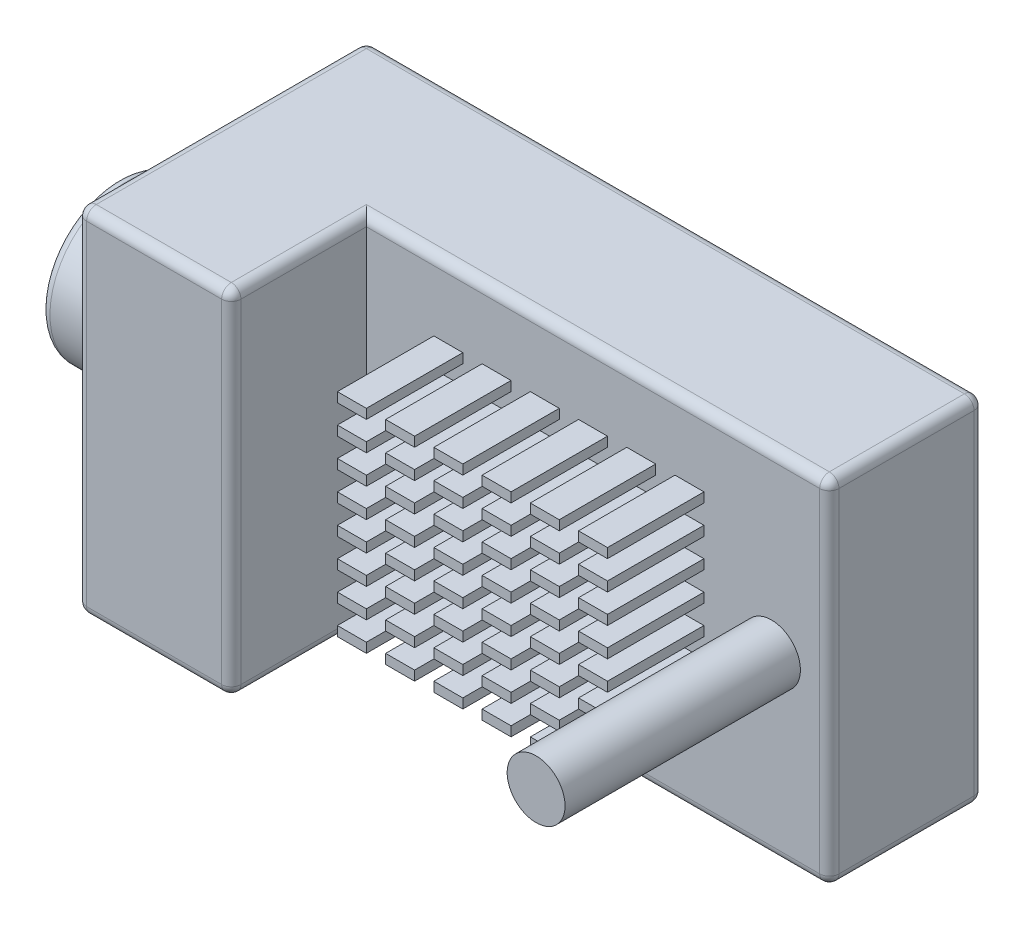
SolidWorks part; units mm, degrees
ref_plane "前基準面" through (0, 0, 0) normal (0, 0, 1) x (1, 0, 0)
ref_plane "上基準面" through (0, 0, 0) normal (0, 1, 0) x (1, 0, 0)
ref_plane "右基準面" through (0, 0, 0) normal (1, 0, 0) x (0, 0, -1)
sketch "草圖1" plane through (0, 0, 0) normal (0, 0, 1) x (1, 0, 0)
  line L1 (-16, 9.15) -> (16, 9.15)
  line L2 (-16, 9.15) -> (-16, -9.15)
  line L3 (-16, -9.15) -> (16, -9.15)
  line L4 (16, 9.15) -> (16, -9.15)
  line L5 (-16, 9.15) -> (16, -9.15) construction
  line L6 (-16, -9.15) -> (16, 9.15) construction
  point P0 (0, 0)
  dimension "D1" = 18.3
  dimension "D2" = 32
extrude "填料-伸長1" add sketch "草圖1" along normal mid plane 8
sketch "草圖2" plane through (0, 0, 4) normal (0, 0, 1) x (1, 0, 0)
  line L0 (-16, -9.15) -> (16, -9.15) construction
  line L1 (-16, 9.15) -> (-8, 9.15)
  line L2 (-16, 9.15) -> (-16, -9.15)
  line L3 (-16, -9.15) -> (-8, -9.15)
  line L4 (-8, 9.15) -> (-8, -9.15)
  dimension "D1" = 8
extrude "填料-伸長2" add sketch "草圖2" along normal blind 7
sketch "草圖4" plane through (-16, 0, 0) normal (-1, 0, 0) x (0, 0, 1)
  line L0 (11, 9.15) -> (11, -9.15) construction
  line L1 (11, -9.15) -> (-4, -9.15) construction
  circle A0 centre (3.5, 0) radius 2.5
  point P4 (11, 0)
  point P7 (3.5, -9.15)
  dimension "D1" = 5
extrude "填料-伸長3" add sketch "草圖4" along normal blind 2
sketch "草圖5" plane through (-18, 0, 0) normal (-1, 0, 0) x (0, 0, 1)
  circle A0 centre (3.5, 0) radius 4
  dimension "D1" = 8
extrude "填料-伸長4" add sketch "草圖5" along normal blind 3.4
sketch "草圖6" plane through (0, 0, 4) normal (0, 0, 1) x (1, 0, 0)
  line L0 (-8, -9.15) -> (-8, 9.15) construction
  line L1 (-5, 6) -> (10, 6)
  line L2 (-5, 6) -> (-5, -6)
  line L3 (-5, -6) -> (10, -6)
  line L4 (10, 6) -> (10, -6)
  line L5 (-5, 6) -> (10, -6) construction
  line L6 (-5, -6) -> (10, 6) construction
  line L7 (16, -9.15) -> (16, 9.15) construction
  point P0 (2.5, 0)
  point P9 (16, 0)
  dimension "D1" = 15
  dimension "D2" = 12
  dimension "D3" = 3
extrude "填料-伸長5" add sketch "草圖6" along normal blind 5
sketch "草圖7" plane through (0, 0, 9) normal (0, 0, 1) x (1, 0, 0)
  line L0 (-2, 5.5) -> (-2, 5)
  line L1 (-4.5, 5.5) -> (-3, 5.5)
  line L2 (-4.5, 5.5) -> (-4.5, 5)
  line L3 (-4.5, 5) -> (-3, 5)
  line L4 (-3, 5.5) -> (-3, 5)
  line L5 (-2, 5.5) -> (-0.5, 5.5)
  line L6 (-0.5, 5.5) -> (-0.5, 5)
  line L7 (-2, 5) -> (-0.5, 5)
  line L8 (0.5, 5.5) -> (0.5, 5)
  line L9 (0.5, 5.5) -> (2, 5.5)
  line L10 (2, 5.5) -> (2, 5)
  line L11 (0.5, 5) -> (2, 5)
  line L12 (3, 5.5) -> (3, 5)
  line L13 (3, 5.5) -> (4.5, 5.5)
  line L14 (4.5, 5.5) -> (4.5, 5)
  line L15 (3, 5) -> (4.5, 5)
  line L16 (5.5, 5.5) -> (5.5, 5)
  line L17 (5.5, 5.5) -> (7, 5.5)
  line L18 (7, 5.5) -> (7, 5)
  line L19 (5.5, 5) -> (7, 5)
  line L20 (8, 5.5) -> (8, 5)
  line L21 (8, 5.5) -> (9.5, 5.5)
  line L22 (9.5, 5.5) -> (9.5, 5)
  line L23 (8, 5) -> (9.5, 5)
  line L24 (-4.5, 4) -> (-4.5, 3.5)
  line L25 (-4.5, 4) -> (-3, 4)
  line L26 (-3, 4) -> (-3, 3.5)
  line L27 (-4.5, 3.5) -> (-3, 3.5)
  line L28 (-2, 4) -> (-2, 3.5)
  line L29 (-2, 3.5) -> (-0.5, 3.5)
  line L30 (-0.5, 4) -> (-0.5, 3.5)
  line L31 (-2, 4) -> (-0.5, 4)
  line L32 (0.5, 4) -> (0.5, 3.5)
  line L33 (0.5, 3.5) -> (2, 3.5)
  line L34 (2, 4) -> (2, 3.5)
  line L35 (0.5, 4) -> (2, 4)
  line L36 (3, 4) -> (3, 3.5)
  line L37 (3, 3.5) -> (4.5, 3.5)
  line L38 (4.5, 4) -> (4.5, 3.5)
  line L39 (3, 4) -> (4.5, 4)
  line L40 (5.5, 4) -> (5.5, 3.5)
  line L41 (5.5, 3.5) -> (7, 3.5)
  line L42 (7, 4) -> (7, 3.5)
  line L43 (5.5, 4) -> (7, 4)
  line L44 (8, 4) -> (8, 3.5)
  line L45 (8, 3.5) -> (9.5, 3.5)
  line L46 (9.5, 4) -> (9.5, 3.5)
  line L47 (8, 4) -> (9.5, 4)
  line L48 (-4.5, 2.5) -> (-4.5, 2)
  line L49 (-4.5, 2.5) -> (-3, 2.5)
  line L50 (-3, 2.5) -> (-3, 2)
  line L51 (-4.5, 2) -> (-3, 2)
  line L52 (-2, 2.5) -> (-2, 2)
  line L53 (-2, 2) -> (-0.5, 2)
  line L54 (-0.5, 2.5) -> (-0.5, 2)
  line L55 (-2, 2.5) -> (-0.5, 2.5)
  line L56 (0.5, 2.5) -> (0.5, 2)
  line L57 (0.5, 2) -> (2, 2)
  line L58 (2, 2.5) -> (2, 2)
  line L59 (0.5, 2.5) -> (2, 2.5)
  line L60 (3, 2.5) -> (3, 2)
  line L61 (3, 2) -> (4.5, 2)
  line L62 (4.5, 2.5) -> (4.5, 2)
  line L63 (3, 2.5) -> (4.5, 2.5)
  line L64 (5.5, 2.5) -> (5.5, 2)
  line L65 (5.5, 2) -> (7, 2)
  line L66 (7, 2.5) -> (7, 2)
  line L67 (5.5, 2.5) -> (7, 2.5)
  line L68 (8, 2.5) -> (8, 2)
  line L69 (8, 2) -> (9.5, 2)
  line L70 (9.5, 2.5) -> (9.5, 2)
  line L71 (8, 2.5) -> (9.5, 2.5)
  line L72 (-4.5, 1) -> (-4.5, 0.5)
  line L73 (-4.5, 1) -> (-3, 1)
  line L74 (-3, 1) -> (-3, 0.5)
  line L75 (-4.5, 0.5) -> (-3, 0.5)
  line L76 (-2, 1) -> (-2, 0.5)
  line L77 (-2, 0.5) -> (-0.5, 0.5)
  line L78 (-0.5, 1) -> (-0.5, 0.5)
  line L79 (-2, 1) -> (-0.5, 1)
  line L80 (0.5, 1) -> (0.5, 0.5)
  line L81 (0.5, 0.5) -> (2, 0.5)
  line L82 (2, 1) -> (2, 0.5)
  line L83 (0.5, 1) -> (2, 1)
  line L84 (3, 1) -> (3, 0.5)
  line L85 (3, 0.5) -> (4.5, 0.5)
  line L86 (4.5, 1) -> (4.5, 0.5)
  line L87 (3, 1) -> (4.5, 1)
  line L88 (5.5, 1) -> (5.5, 0.5)
  line L89 (5.5, 0.5) -> (7, 0.5)
  line L90 (7, 1) -> (7, 0.5)
  line L91 (5.5, 1) -> (7, 1)
  line L92 (8, 1) -> (8, 0.5)
  line L93 (8, 0.5) -> (9.5, 0.5)
  line L94 (9.5, 1) -> (9.5, 0.5)
  line L95 (8, 1) -> (9.5, 1)
  line L96 (-4.5, -0.5) -> (-4.5, -1)
  line L97 (-4.5, -0.5) -> (-3, -0.5)
  line L98 (-3, -0.5) -> (-3, -1)
  line L99 (-4.5, -1) -> (-3, -1)
  line L100 (-2, -0.5) -> (-2, -1)
  line L101 (-2, -1) -> (-0.5, -1)
  line L102 (-0.5, -0.5) -> (-0.5, -1)
  line L103 (-2, -0.5) -> (-0.5, -0.5)
  line L104 (0.5, -0.5) -> (0.5, -1)
  line L105 (0.5, -1) -> (2, -1)
  line L106 (2, -0.5) -> (2, -1)
  line L107 (0.5, -0.5) -> (2, -0.5)
  line L108 (3, -0.5) -> (3, -1)
  line L109 (3, -1) -> (4.5, -1)
  line L110 (4.5, -0.5) -> (4.5, -1)
  line L111 (3, -0.5) -> (4.5, -0.5)
  line L112 (5.5, -0.5) -> (5.5, -1)
  line L113 (5.5, -1) -> (7, -1)
  line L114 (7, -0.5) -> (7, -1)
  line L115 (5.5, -0.5) -> (7, -0.5)
  line L116 (8, -0.5) -> (8, -1)
  line L117 (8, -1) -> (9.5, -1)
  line L118 (9.5, -0.5) -> (9.5, -1)
  line L119 (8, -0.5) -> (9.5, -0.5)
  line L120 (-4.5, -2) -> (-4.5, -2.5)
  line L121 (-4.5, -2) -> (-3, -2)
  line L122 (-3, -2) -> (-3, -2.5)
  line L123 (-4.5, -2.5) -> (-3, -2.5)
  line L124 (-2, -2) -> (-2, -2.5)
  line L125 (-2, -2.5) -> (-0.5, -2.5)
  line L126 (-0.5, -2) -> (-0.5, -2.5)
  line L127 (-2, -2) -> (-0.5, -2)
  line L128 (0.5, -2) -> (0.5, -2.5)
  line L129 (0.5, -2.5) -> (2, -2.5)
  line L130 (2, -2) -> (2, -2.5)
  line L131 (0.5, -2) -> (2, -2)
  line L132 (3, -2) -> (3, -2.5)
  line L133 (3, -2.5) -> (4.5, -2.5)
  line L134 (4.5, -2) -> (4.5, -2.5)
  line L135 (3, -2) -> (4.5, -2)
  line L136 (5.5, -2) -> (5.5, -2.5)
  line L137 (5.5, -2.5) -> (7, -2.5)
  line L138 (7, -2) -> (7, -2.5)
  line L139 (5.5, -2) -> (7, -2)
  line L140 (8, -2) -> (8, -2.5)
  line L141 (8, -2.5) -> (9.5, -2.5)
  line L142 (9.5, -2) -> (9.5, -2.5)
  line L143 (8, -2) -> (9.5, -2)
  line L144 (-4.5, -3.5) -> (-4.5, -4)
  line L145 (-4.5, -3.5) -> (-3, -3.5)
  line L146 (-3, -3.5) -> (-3, -4)
  line L147 (-4.5, -4) -> (-3, -4)
  line L148 (-2, -3.5) -> (-2, -4)
  line L149 (-2, -4) -> (-0.5, -4)
  line L150 (-0.5, -3.5) -> (-0.5, -4)
  line L151 (-2, -3.5) -> (-0.5, -3.5)
  line L152 (0.5, -3.5) -> (0.5, -4)
  line L153 (0.5, -4) -> (2, -4)
  line L154 (2, -3.5) -> (2, -4)
  line L155 (0.5, -3.5) -> (2, -3.5)
  line L156 (3, -3.5) -> (3, -4)
  line L157 (3, -4) -> (4.5, -4)
  line L158 (4.5, -3.5) -> (4.5, -4)
  line L159 (3, -3.5) -> (4.5, -3.5)
  line L160 (5.5, -3.5) -> (5.5, -4)
  line L161 (5.5, -4) -> (7, -4)
  line L162 (7, -3.5) -> (7, -4)
  line L163 (5.5, -3.5) -> (7, -3.5)
  line L164 (8, -3.5) -> (8, -4)
  line L165 (8, -4) -> (9.5, -4)
  line L166 (9.5, -3.5) -> (9.5, -4)
  line L167 (8, -3.5) -> (9.5, -3.5)
  line L168 (-4.5, -5) -> (-4.5, -5.5)
  line L169 (-4.5, -5) -> (-3, -5)
  line L170 (-3, -5) -> (-3, -5.5)
  line L171 (-4.5, -5.5) -> (-3, -5.5)
  line L172 (-2, -5) -> (-2, -5.5)
  line L173 (-2, -5.5) -> (-0.5, -5.5)
  line L174 (-0.5, -5) -> (-0.5, -5.5)
  line L175 (-2, -5) -> (-0.5, -5)
  line L176 (0.5, -5) -> (0.5, -5.5)
  line L177 (0.5, -5.5) -> (2, -5.5)
  line L178 (2, -5) -> (2, -5.5)
  line L179 (0.5, -5) -> (2, -5)
  line L180 (3, -5) -> (3, -5.5)
  line L181 (3, -5.5) -> (4.5, -5.5)
  line L182 (4.5, -5) -> (4.5, -5.5)
  line L183 (3, -5) -> (4.5, -5)
  line L184 (5.5, -5) -> (5.5, -5.5)
  line L185 (5.5, -5.5) -> (7, -5.5)
  line L186 (7, -5) -> (7, -5.5)
  line L187 (5.5, -5) -> (7, -5)
  line L188 (8, -5) -> (8, -5.5)
  line L189 (8, -5.5) -> (9.5, -5.5)
  line L190 (9.5, -5) -> (9.5, -5.5)
  line L191 (8, -5) -> (9.5, -5)
  line L192 (-5, 6) -> (-5, -6) construction
  line L193 (10, 6) -> (-5, 6) construction
  line L195 (-5, 6) -> (10, 6)
  line L196 (-5, 6) -> (-5, -6)
  line L197 (-5, -6) -> (10, -6)
  line L198 (10, 6) -> (10, -6)
  point P29 (-2, 5.25)
  dimension "D1" = 1.5
  dimension "D2" = 0.5
  dimension "D4" = 1
  dimension "D6" = 1
  dimension "D7" = 0.5
  dimension "D8" = 0.5
  dimension "D3" = 6
  dimension "D5" = 8
extrude "除料-伸長1" cut sketch "草圖7" against normal blind 5
sketch "草圖8" plane through (0, 0, 4) normal (0, 0, 1) x (1, 0, 0)
  line L0 (16, -9.15) -> (16, 9.15) construction
  circle A0 centre (13, 0) radius 1.5
  point P4 (16, 0)
  dimension "D1" = 3
  dimension "D2" = 3
extrude "填料-伸長6" add sketch "草圖8" along normal blind 12.2
fillet "圓角1" radius 0.5 18 edges at (-16, 9.15, 3.5) (-16, 0, -4) (-16, -2.5, 3.5) (-16, -9.15, 3.5) (-8, -9.15, 7.5) (4, -9.15, 4) (16, -9.15, 0) (0, -9.15, -4) (-12, 9.15, 11) (-8, 0, 11) (-12, -9.15, 11) (-16, 0, 11) (4, 9.15, 4) (-8, 9.15, 7.5) (0, 9.15, -4) (16, 0, 4) (16, 9.15, 0) (16, 0, -4)
fillet "圓角2" radius 0.5 3 edges at (-18, -2.5, 3.5) (-18, -4, 3.5) (-21.4, -4, 3.5)
